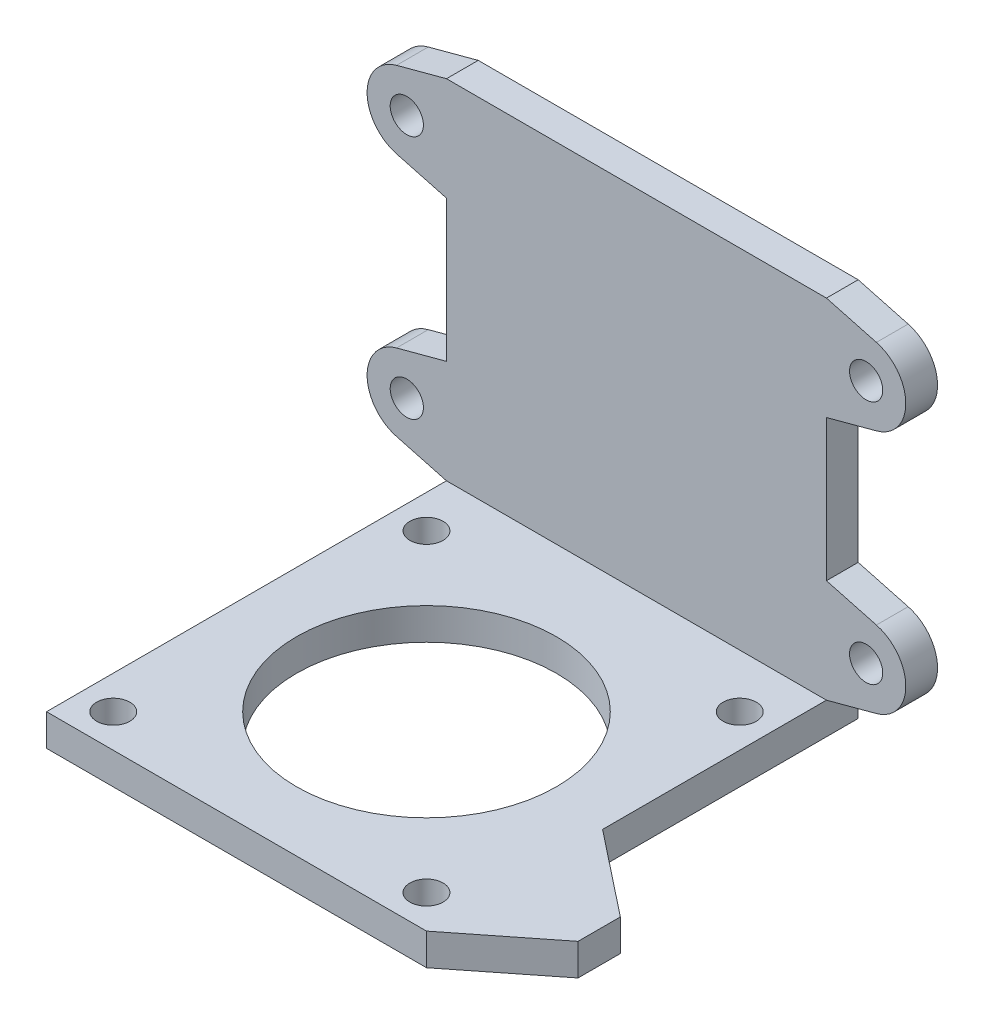
SolidWorks part; units mm, degrees
material "PC High Viscosity"
ref_plane "Front Plane" through (0, 0, 0) normal (0, 0, 1) x (1, 0, 0)
ref_plane "Top Plane" through (0, 0, 0) normal (0, 1, 0) x (1, 0, 0)
ref_plane "Right Plane" through (0, 0, 0) normal (1, 0, 0) x (0, 0, -1)
sketch "Sketch1" plane through (0, 0, 0) normal (0, 0, 1) x (1, 0, 0)
  line L1 (-28.5, 28.5) -> (28.5, 28.5)
  line L2 (-28.5, 28.5) -> (-28.5, -28.5)
  line L3 (-28.5, -28.5) -> (28.5, -28.5)
  line L4 (28.5, 28.5) -> (28.5, -28.5)
  line L5 (-28.5, 28.5) -> (28.5, -28.5) construction
  line L6 (-28.5, -28.5) -> (28.5, 28.5) construction
  point P0 (0, 0)
  dimension "D1" = 57
extrude "Boss-Extrude1" add sketch "Sketch1" along normal blind 4.7625
sketch "Sketch2" plane through (0, 0, 4.7625) normal (0, 0, 1) x (1, 0, 0)
  line L0 (28.5, -28.5) -> (28.5, 28.5) construction
  line L1 (-28.5, -28.5) -> (28.5, -28.5)
  line L2 (-28.5, -28.5) -> (-28.5, -23.7375)
  line L3 (-28.5, -23.7375) -> (28.5, -23.7375)
  line L4 (28.5, -28.5) -> (28.5, -23.7375)
  dimension "D1" = 4.7625
extrude "Boss-Extrude2" add sketch "Sketch2" along normal blind 60
sketch "Sketch3" plane through (0, -23.7375, 0) normal (0, 1, 0) x (1, 0, 0)
  line L0 (-28.5, -7.7625) -> (28.5, -7.7625) construction
  line L1 (-28.5, -64.7625) -> (-28.5, -4.7625) construction
  line L2 (28.5, -64.7625) -> (28.5, -4.7625) construction
  line L3 (28.5, -64.7625) -> (-28.5, -64.7625) construction
  line L4 (-28.5, -64.7625) -> (28.5, -7.7625) construction
  circle A0 centre (0, -36.2625) radius 19.5
  dimension "D2" = 39
  dimension "D1" = 57
extrude "Cut-Extrude1" cut sketch "Sketch3" against normal through all
hole_wizard "#10 Clearance Hole1" positions "Sketch4" profile "Sketch5" hole size "#10" standard "ANSI Inch" end condition through all
sketch "Sketch4" plane through (0, -28.5, 0) normal (0, -1, 0) x (-1, 0, 0)
  line L1 (23.495, -59.7575) -> (-23.495, -59.7575) construction
  line L2 (23.495, -59.7575) -> (23.495, -12.7675) construction
  line L3 (23.495, -12.7675) -> (-23.495, -12.7675) construction
  line L4 (-23.495, -59.7575) -> (-23.495, -12.7675) construction
  line L5 (23.495, -59.7575) -> (-23.495, -12.7675) construction
  line L6 (23.495, -12.7675) -> (-23.495, -59.7575) construction
  point P1 (0, -36.2625)
  point P2 (-23.495, -12.7675)
  point P115 (23.495, -59.7575)
  point P116 (23.495, -12.7675)
  point P117 (-23.495, -59.7575)
  dimension "D1" = 46.99
sketch "Sketch5" plane through (0, -28.5, 36.2625) normal (1, 0, 0) x (0, 0, -1)
  line L0 (0, 0) -> (0, 57)
  line L1 (0, 57) -> (2.4892, 57)
  line L2 (2.4892, 57) -> (2.4892, 0)
  line L5 (2.4892, 0) -> (0, 0)
  line L11 (0, -6.35) -> (0, 107.95) construction
  dimension "Thru Hole Dia." = 4.9784
  dimension "Thru Hole Depth" = 57
sketch "Sketch7" plane through (0, 0, 0) normal (0, 0, 1) x (1, 0, 0)
  line L0 (28.5, -23.7375) -> (28.5, 28.5) construction
  line L5 (28.5, -23.7375) -> (35.9939, -21.7295)
  line L6 (-34.4531, 20.7417) -> (34.4531, 20.7417) construction
  line L7 (-34.4531, 20.7417) -> (-34.4531, -15.9792) construction
  line L9 (-34.4531, -15.9792) -> (34.4531, -15.9792) construction
  line L10 (28.5, -23.7375) -> (-28.5, 28.5) construction
  line L11 (34.4531, 20.7417) -> (34.4531, -15.9792) construction
  line L12 (-34.4531, 20.7417) -> (34.4531, -15.9792) construction
  line L13 (-34.4531, -15.9792) -> (34.4531, 20.7417) construction
  line L14 (28.5, -8.221) -> (35.9939, -10.229)
  line L15 (28.5, -23.7375) -> (28.5, -8.221)
  line L16 (28.5, 2.3813) -> (-28.5, 2.3812) construction
  line L17 (-28.5, 28.5) -> (-28.5, -23.7375) construction
  line L18 (0, -15.9792) -> (0, 20.7417) construction
  line L19 (28.5, 12.9835) -> (35.9939, 14.9915)
  line L20 (28.5, 28.5) -> (35.9939, 26.492)
  line L21 (28.5, 28.5) -> (28.5, 12.9835)
  line L22 (-28.5, 28.5) -> (-28.5, 12.9835)
  line L23 (-28.5, 28.5) -> (-35.9939, 26.492)
  line L24 (-28.5, 12.9835) -> (-35.9939, 14.9915)
  line L25 (-28.5, -23.7375) -> (-35.9939, -21.7295)
  line L26 (-28.5, -8.221) -> (-35.9939, -10.229)
  line L27 (-28.5, -23.7375) -> (-28.5, -8.221)
  arc A1 (35.9939, -21.7295) -> (35.9939, -10.229) centre (34.4531, -15.9792) ccw
  arc A2 (35.9939, 26.492) -> (35.9939, 14.9915) centre (34.4531, 20.7417) cw
  arc A3 (-35.9939, 26.492) -> (-35.9939, 14.9915) centre (-34.4531, 20.7417) ccw
  arc A4 (-35.9939, -21.7295) -> (-35.9939, -10.229) centre (-34.4531, -15.9792) cw
  point P0 (0, 0)
  point P1 (0, 2.3813)
  dimension "D1" = 5.9531
  dimension "D3" = 75
  dimension "D4" = 75
extrude "Boss-Extrude3" add sketch "Sketch7" along normal blind 4.7625
hole_wizard "#10 Clearance Hole2" positions "Sketch8" profile "Sketch9" hole size "#10" standard "ANSI Inch" end condition through all
sketch "Sketch8" plane through (0, 0, 4.7625) normal (0, 0, 1) x (1, 0, 0)
  point P0 (34.4531, -15.9792)
  point P3 (34.4531, 20.7417)
  point P6 (-34.4531, 20.7417)
  point P9 (-34.4531, -15.9792)
sketch "Sketch9" plane through (34.4531, -15.9792, 4.7625) normal (1, 0, 0) x (0, -1, 0)
  line L0 (0, 0) -> (0, 4.7625)
  line L1 (0, 4.7625) -> (2.4892, 4.7625)
  line L2 (2.4892, 4.7625) -> (2.4892, 0)
  line L5 (2.4892, 0) -> (0, 0)
  line L11 (0, -6.35) -> (0, 107.95) construction
  dimension "Thru Hole Dia." = 4.9784
  dimension "Thru Hole Depth" = 4.7625
fillet "Fillet1" [suppressed] radius 0.5
sketch "Sketch10" plane through (0, -28.5, 0) normal (0, -1, 0) x (1, 0, 0)
  line L0 (0, 48.3795) -> (-28.5, 48.3795) construction
  line L1 (28.5, 64.7625) -> (28.5, 0) construction
  line L2 (-28.5, 64.7625) -> (-28.5, 0) construction
  line L3 (-28.5, 64.7625) -> (28.5, 64.7625) construction
  line L4 (0, 48.3795) -> (0, 64.7625) construction
  line L8 (41.2, 48.3795) -> (41.2, 54.7295)
  line L13 (41.2, 48.3795) -> (28.5, 38.3465)
  line L14 (41.2, 54.7295) -> (28.5, 64.7625)
  line L16 (28.5, 64.7625) -> (28.5, 38.3465)
  dimension "D1" = 16.383
  dimension "D2" = 12.7
  dimension "D3" = 6.35
extrude "Boss-Extrude4" add sketch "Sketch10" against normal blind 4.7625
